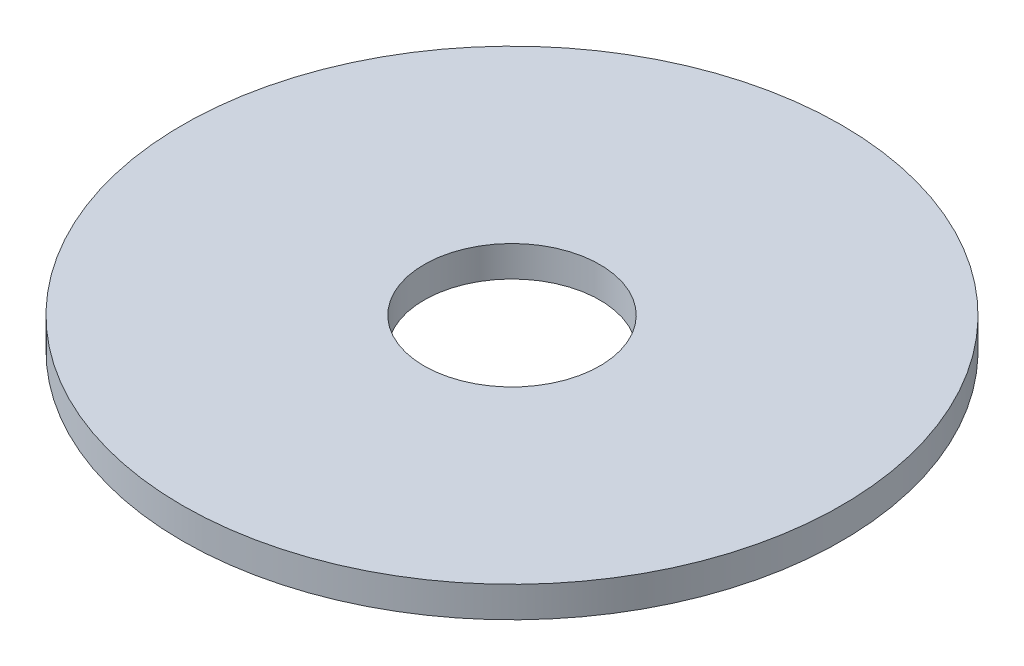
SolidWorks part; units mm, degrees
ref_plane "Front Plane" through (0, 0, 0) normal (0, 0, 1) x (1, 0, 0)
ref_plane "Top Plane" through (0, 0, 0) normal (0, 1, 0) x (1, 0, 0)
ref_plane "Right Plane" through (0, 0, 0) normal (1, 0, 0) x (0, 0, -1)
sketch "Sketch1" plane through (0, 0, 0) normal (0, 1, 0) x (1, 0, 0)
  circle A0 centre (0, 0) radius 15
  circle A1 centre (0, 0) radius 4
extrude "Boss-Extrude1" add sketch "Sketch1" along normal blind 1.4
